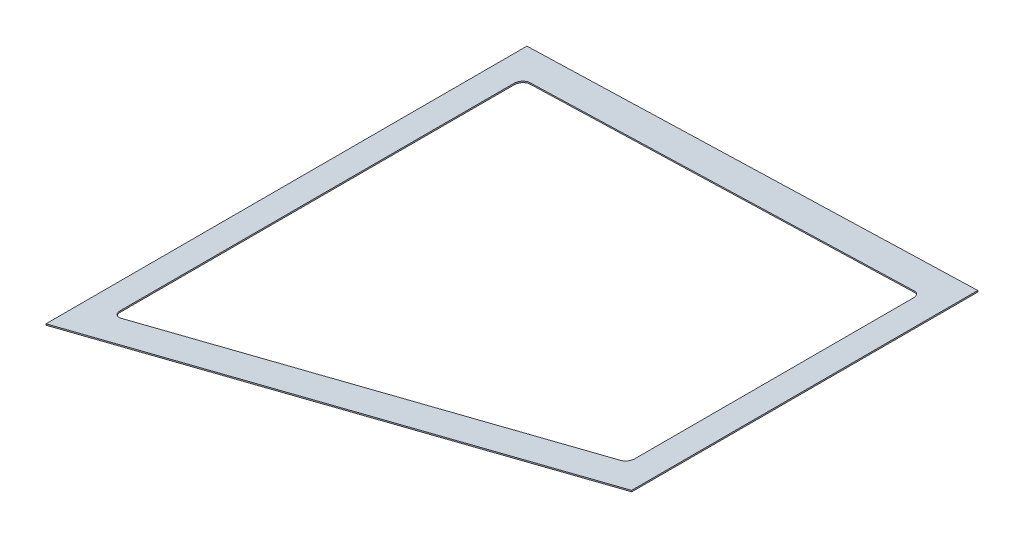
SolidWorks part; units mm, degrees
material "Plain Carbon Steel"
ref_plane "Front Plane" through (0, 0, 0) normal (0, 0, 1) x (1, 0, 0)
ref_plane "Top Plane" through (0, 0, 0) normal (0, 1, 0) x (1, 0, 0)
ref_plane "Right Plane" through (0, 0, 0) normal (1, 0, 0) x (0, 0, -1)
ref_plane "Plane1" through (40.7219, -259.9314, 0) normal (0.1548, -0.9879, 0) x (0.9879, 0.1548, 0)
sketch "Sketch1" plane through (40.7219, -259.9314, 0) normal (0.1548, -0.9879, 0) x (0.9879, 0.1548, 0)
  line L0 (2473.917, -58.4448) -> (2473.917, -112.6257)
  line L2 (2468.6809, -118.5768) -> (2106.7519, -165.0348)
  line L4 (2498.917, -58.4448) -> (2498.917, -139.9008)
  line L6 (2498.917, -139.9008) -> (2074.988, -194.3172)
  line L31 (2074.988, 194.3172) -> (2074.988, 0)
  line L32 (2498.917, 139.9008) -> (2074.988, 194.3172)
  line L33 (2498.917, 0) -> (2498.917, 58.4448)
  line L34 (2498.917, 58.4448) -> (2498.917, 139.9008)
  line L35 (2074.988, 194.3172) -> (2074.988, -194.3172)
  line L36 (2498.917, 139.9008) -> (2074.988, 194.3172)
  line L37 (2498.917, -58.4448) -> (2498.917, 58.4448)
  line L38 (2498.917, 58.4448) -> (2498.917, 139.9008)
  line L45 (-0.4745, 0) -> (3081.9628, 0) construction
  line L49 (2099.988, 165.903) -> (2099.988, 0)
  line L50 (2473.917, 117.9047) -> (2099.988, 165.903)
  line L51 (2473.917, 58.4448) -> (2473.917, 117.9047)
  line L52 (2473.917, 0) -> (2473.917, 58.4448)
  line L53 (2099.988, 159.0836) -> (2099.988, -159.0836)
  line L54 (2468.6809, 118.5768) -> (2106.7519, 165.0348)
  line L55 (2473.917, 58.4448) -> (2473.917, 112.6257)
  line L56 (2473.917, -58.4448) -> (2473.917, 58.4448)
  arc A0 (2468.6809, 118.5768) -> (2473.917, 112.6257) centre (2467.917, 112.6257) cw
  arc A1 (2099.988, 159.0836) -> (2106.7519, 165.0348) centre (2105.988, 159.0836) cw
  arc A2 (2099.988, -159.0836) -> (2106.7519, -165.0348) centre (2105.988, -159.0836) ccw
  arc A3 (2468.6809, -118.5768) -> (2473.917, -112.6257) centre (2467.917, -112.6257) ccw
  dimension "D2" = 30
  dimension "D3" = 6
  dimension "D1" = 5
extrude "Boss-Extrude1" add sketch "Sketch1" along normal blind 1
